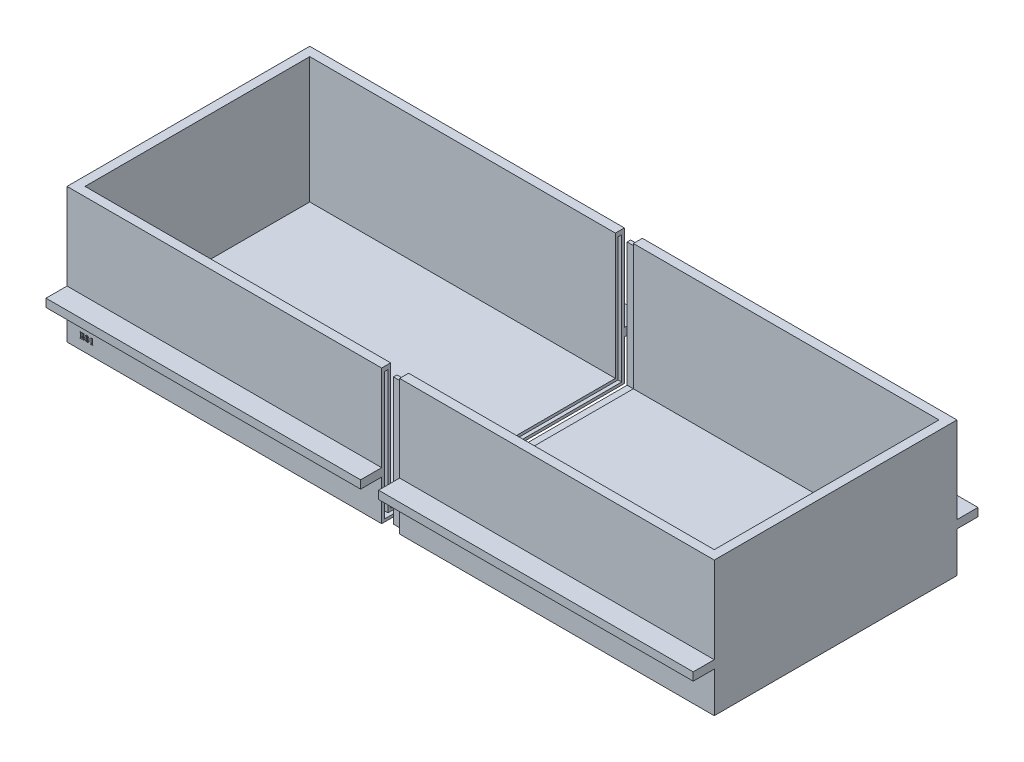
SolidWorks part; units mm, degrees
ref_plane "Front Plane" through (0, 0, 0) normal (0, 0, 1) x (1, 0, 0)
ref_plane "Top Plane" through (0, 0, 0) normal (0, 1, 0) x (1, 0, 0)
ref_plane "Right Plane" through (0, 0, 0) normal (1, 0, 0) x (0, 0, -1)
sketch "Sketch1" plane through (0, 0, 0) normal (0, 1, 0) x (1, 0, 0)
  line L1 (0, 0) -> (175, 0)
  line L2 (0, 0) -> (0, 135)
  line L3 (0, 135) -> (175, 135)
  line L4 (175, 0) -> (175, 135)
  dimension "D1" = 135
  dimension "D2" = 175
extrude "Boss-Extrude2" add sketch "Sketch1" along normal blind 75 contours L3 L4 L1 L2
sketch "Sketch3" plane through (0, 75, 0) normal (0, 1, 0) x (1, 0, 0)
  line L0 (0, 0) -> (0, 135) construction
  line L1 (0, 5) -> (170, 5)
  line L2 (0, 5) -> (0, 130)
  line L3 (0, 130) -> (170, 130)
  line L4 (170, 5) -> (170, 130)
  line L5 (175, 0) -> (175, 135) construction
  line L6 (0, 0) -> (175, 0) construction
  line L7 (0, 135) -> (175, 135) construction
  dimension "D1" = 0
  dimension "D2" = 5
  dimension "D3" = 5
  dimension "D4" = 5
extrude "Cut-Extrude3" cut sketch "Sketch3" against normal blind 70 contours L3 L4 L1 L2
sketch "Sketch5" plane through (0, 0, 0) normal (-1, 0, 0) x (0, 0, 1)
  line L0 (-132.5, 72.5) -> (-132.5, 2.5)
  line L1 (0, 0) -> (-135, 0) construction
  line L2 (-130, 75) -> (-135, 75) construction
  line L3 (-2.5, 72.5) -> (-2.5, 2.5)
  line L4 (-132.5, 2.5) -> (-2.5, 2.5)
  dimension "D1" = 2.5
  dimension "D2" = 2.5
extrude "Extrude-Thin4" add sketch "Sketch5" along normal blind 5 draft 0.5 and the other way blind 1 draft 1 separate body thin
mirror "Mirror7" about plane through (-5, 0, 0) normal (1, 0, 0) of bodies 106
sketch "Sketch11" plane through (-10, 0, 0) normal (1, 0, 0) x (0, 0, -1)
  line L0 (2.5, 72.5) -> (2.5, 2.5)
  line L1 (0, 0) -> (135, 0) construction
  line L2 (0, 75) -> (5, 75) construction
  line L3 (132.5, 72.5) -> (132.5, 2.5)
  line L4 (132.5, 2.5) -> (2.5, 2.5)
  dimension "D1" = 2.5
  dimension "D2" = 2.5
extrude "Cut-Extrude-Thin1" cut sketch "Sketch11" against normal blind 5 and the other way through all thin thin type two direction wall 1 second wall 1
sketch "Sketch13" plane through (0, 0, 0) normal (0, 0, 1) x (1, 0, 0)
  text T0 "E01" font "Stencil" height 3.175
  point P1 (-179.7708, 8.3961)
  point P2 (-171.3575, 10.5417)
  point P3 (-184.5731, 3.8011)
  point P4 (-178.0716, 5.4961)
extrude "Cut-Extrude6" cut sketch "Sketch13" against normal blind 10
sketch "Sketch15" plane through (0, 0, 0) normal (0, 0, 1) x (1, 0, 0)
  line L1 (-185, 75) -> (-185, 0) construction
  line L2 (-10, 75) -> (-10, 0) construction
  line L5 (-185, 22.5) -> (-10, 22.5)
  line L6 (-185, 22.5) -> (-185, 27)
  line L7 (-185, 27) -> (-10, 27)
  line L8 (-10, 22.5) -> (-10, 27)
  dimension "D2" = 4.5
extrude "Boss-Extrude3" add sketch "Sketch15" along normal blind 11.7 contours L7 L8 L5 L6
sketch "Sketch16" plane through (0, 0, 0) normal (0, 0, 1) x (1, 0, 0)
  line L0 (175, 75) -> (175, 0) construction
  line L1 (0, 22.5) -> (175, 22.5)
  line L2 (0, 22.5) -> (0, 27)
  line L3 (0, 27) -> (175, 27)
  line L4 (175, 22.5) -> (175, 27)
extrude "Boss-Extrude4" add sketch "Sketch16" along normal blind 11.7 contours L3 L4 L1 L2
sketch "Sketch17" plane through (0, 0, -135) normal (0, 0, -1) x (-1, 0, 0)
  line L0 (0, 75) -> (0, 0) construction
  line L1 (-175, 27) -> (0, 27)
  line L2 (-175, 27) -> (-175, 22.4963)
  line L3 (-175, 22.4963) -> (0, 22.4963)
  line L4 (0, 27) -> (0, 22.4963)
extrude "Boss-Extrude5" add sketch "Sketch17" along normal blind 11.7
sketch "Sketch18" plane through (0, 0, -135) normal (0, 0, -1) x (-1, 0, 0)
  line L0 (185, 75) -> (185, 0) construction
  line L1 (10, 22.5) -> (185, 22.5)
  line L2 (10, 22.5) -> (10, 27)
  line L3 (10, 27) -> (185, 27)
  line L4 (185, 22.5) -> (185, 27)
  dimension "D1" = 4.5
extrude "Boss-Extrude6" add sketch "Sketch18" along normal blind 11.7
